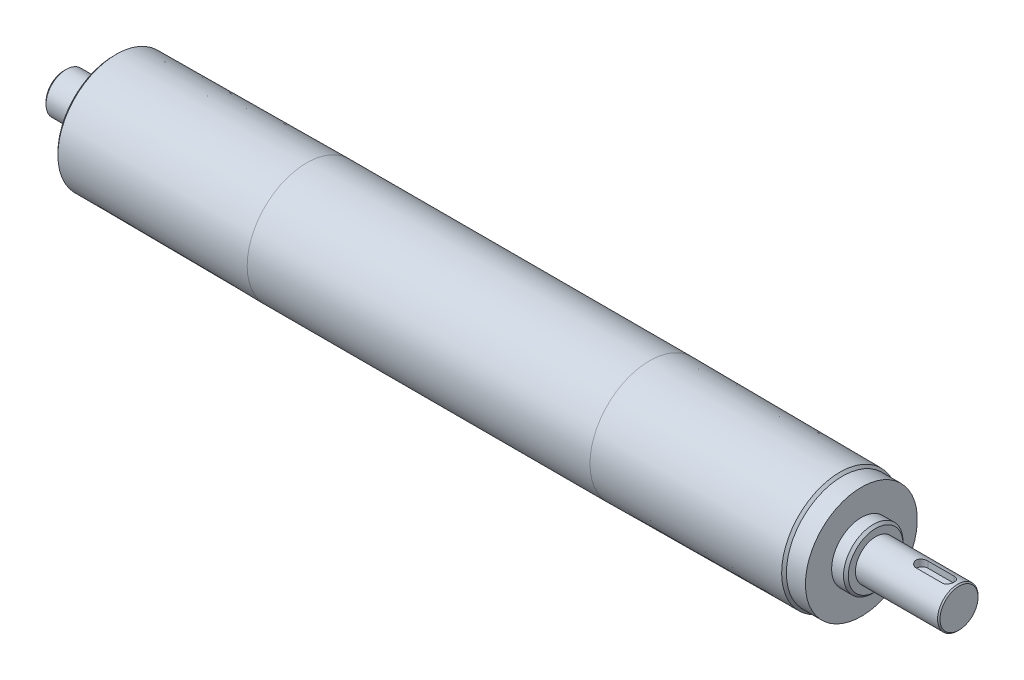
SolidWorks part; units mm, degrees
material "Alloy Steel"
ref_plane "Front Plane" through (0, 0, 0) normal (0, 0, 1) x (1, 0, 0)
ref_plane "Top Plane" through (0, 0, 0) normal (0, 1, 0) x (1, 0, 0)
ref_plane "Right Plane" through (0, 0, 0) normal (1, 0, 0) x (0, 0, -1)
sketch "Sketch1" plane through (0, 0, 0) normal (0, 1, 0) x (1, 0, 0)
  line L0 (-72, 25) -> (72, 25)
  line L1 (0, 0) -> (0, 25) construction
  line L2 (-72, 25) -> (-152, 24.5)
  line L3 (72, 25) -> (152, 24.5)
  line L4 (-174, 0) -> (202, 0)
  line L5 (-152, 24.5) -> (-153, 23.5)
  line L6 (152, 24.5) -> (153, 23.5)
  line L7 (153, 23.5) -> (161, 23.5)
  line L8 (161, 23.5) -> (161, 12.5)
  line L9 (166, 12.5) -> (167, 11.5)
  line L10 (167, 11.5) -> (167, 8.5)
  line L11 (161, 12.5) -> (166, 12.5)
  line L12 (201.5, 8.5) -> (202, 8)
  line L14 (-153, 23.5) -> (-153, 12.5)
  line L15 (-153, 12.5) -> (-157, 12.5)
  line L16 (-157, 12.5) -> (-158, 11.5)
  line L17 (-158, 11.5) -> (-158, 8.5)
  line L18 (-158, 8.5) -> (-173, 8.5)
  line L19 (-173, 8.5) -> (-174, 7.5)
  line L20 (-174, 7.5) -> (-174, 0)
  line L21 (167, 8.5) -> (201.5, 8.5)
  line L22 (202, 8) -> (202, 0)
  dimension "D1" = 25
  dimension "D2" = 80
  dimension "D3" = 80
  dimension "D4" = 24.5
  dimension "D5" = 24.5
  dimension "D6" = 45
  dimension "D7" = 1
  dimension "D8" = 45
  dimension "D9" = 1
  dimension "D10" = 8
  dimension "D11" = 12.5
  dimension "D12" = 5
  dimension "D13" = 1
  dimension "D14" = 8.5
  dimension "D15" = 0.5
  dimension "D16" = 35
  dimension "D17" = 135
  dimension "D18" = 1
  dimension "D19" = 1
  dimension "D20" = 12.5
  dimension "D21" = 8.5
  dimension "D22" = 5
  dimension "D23" = 16
  dimension "D24" = 306
  dimension "D25" = 135
revolve "Revolve1" add sketch "Sketch1" angle 360 about L4
ref_plane "Plane2" through (0, 5.5, 0) normal (0, 1, 0) x (-1, 0, 0)
sketch "Sketch2" plane through (0, 5.5, 0) normal (0, 1, 0) x (-1, 0, 0)
  line L0 (-197.5, 2.5) -> (-186.5, 2.5)
  line L1 (-200, 0) -> (-184, 0) construction
  line L2 (-197.5, -2.5) -> (-186.5, -2.5)
  line L3 (-202, 8) -> (-202, -8) construction
  arc A0 (-197.5, 2.5) -> (-197.5, -2.5) centre (-197.5, 0) ccw
  arc A1 (-186.5, -2.5) -> (-186.5, 2.5) centre (-186.5, 0) ccw
  point P8 (-202, 0)
  dimension "D1" = 2.5
  dimension "D2" = 2.5
  dimension "D3" = 2
  dimension "D4" = 16
extrude "Extrude1" cut sketch "Sketch2" along normal blind 150
